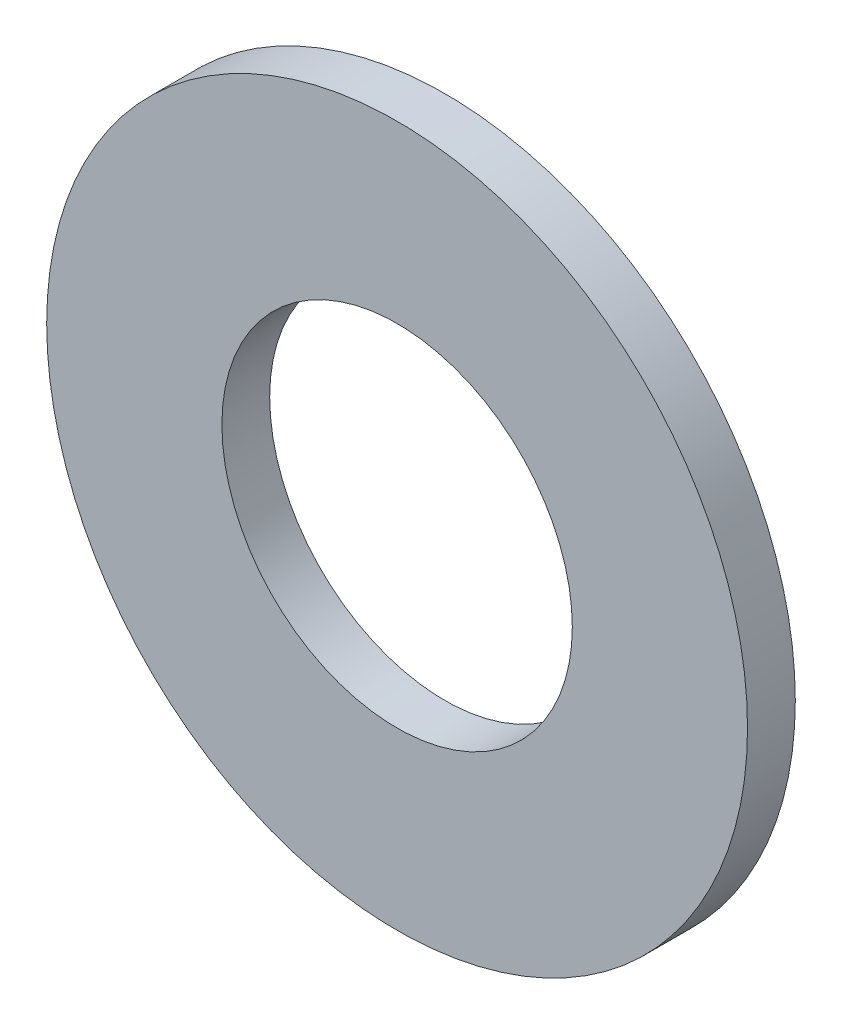
SolidWorks part; units mm, degrees
material "AISI Type 316L stainless steel"
ref_plane "Front Plane" through (0, 0, 0) normal (0, 0, 1) x (1, 0, 0)
ref_plane "Top Plane" through (0, 0, 0) normal (0, 1, 0) x (1, 0, 0)
ref_plane "Right Plane" through (0, 0, 0) normal (1, 0, 0) x (0, 0, -1)
sketch "Sketch1" plane through (0, 0, 0) normal (0, 0, 1) x (1, 0, 0)
  circle A0 centre (0, 0) radius 11
  circle A1 centre (0, 0) radius 5.5
  dimension "D1" = 22
  dimension "D2" = 11
extrude "Boss-Extrude1" add sketch "Sketch1" along normal blind 1.5
